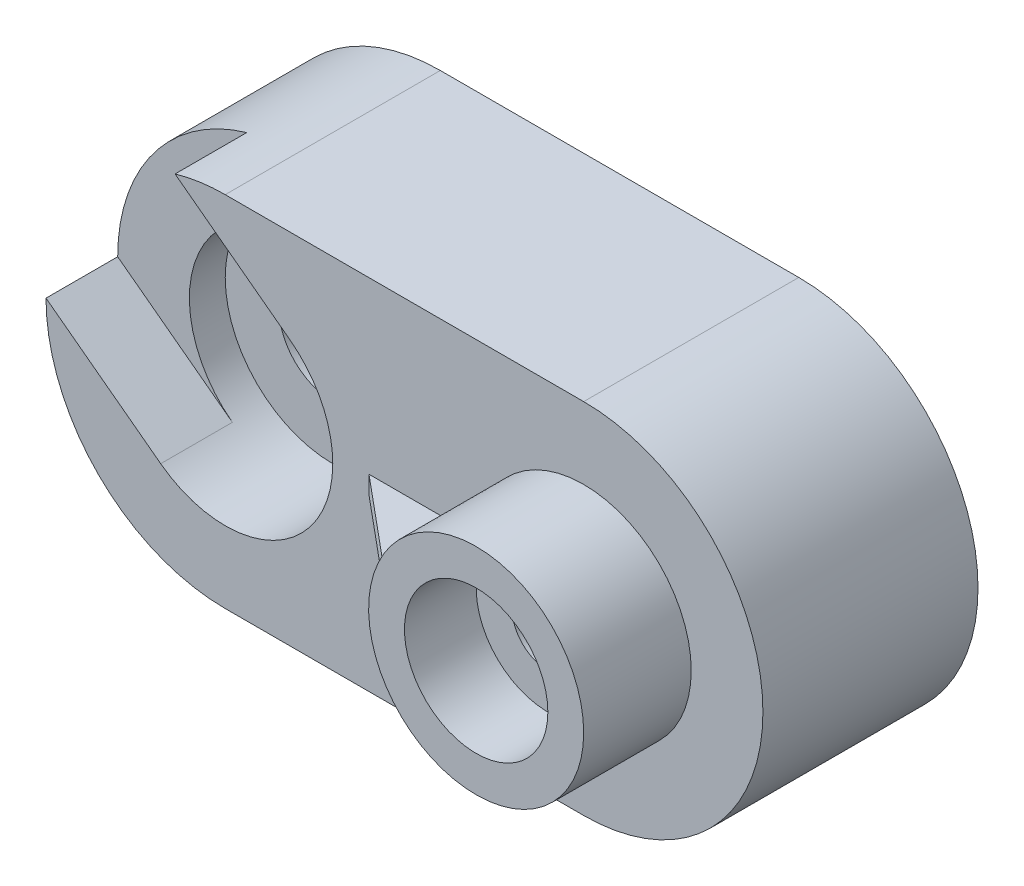
SolidWorks part; units mm, degrees
ref_plane "Front Plane" through (0, 0, 0) normal (0, 0, 1) x (1, 0, 0)
ref_plane "Top Plane" through (0, 0, 0) normal (0, 1, 0) x (1, 0, 0)
ref_plane "Right Plane" through (0, 0, 0) normal (1, 0, 0) x (0, 0, -1)
sketch "Sketch1" plane through (0, 0, 0) normal (0, 0, 1) x (1, 0, 0)
  line L0 (0, 0) -> (100, 0) construction
  line L1 (0, 50) -> (100, 50)
  line L2 (0, -50) -> (100, -50)
  arc A0 (0, 50) -> (0, -50) centre (0, 0) ccw
  arc A1 (100, -50) -> (100, 50) centre (100, 0) ccw
  point P3 (50, 0)
  dimension "D1" = 100
  dimension "D2" = 50
extrude "Boss-Extrude1" add sketch "Sketch1" along normal blind 60
sketch "Sketch2" plane through (0, 0, 0) normal (0, 0, -1) x (-1, 0, 0)
  line L0 (0, 0) -> (-100, 0) construction
  line L1 (0, -30) -> (-100, -30)
  line L2 (0, 30) -> (-100, 30)
  arc A0 (0, -30) -> (0, 30) centre (0, 0) ccw
  arc A1 (-100, 30) -> (-100, -30) centre (-100, 0) ccw
  point P3 (-50, 0)
  dimension "D1" = 100
  dimension "D2" = 30
extrude "Cut-Extrude1" cut sketch "Sketch2" against normal blind 10
sketch "Sketch3" plane through (0, 0, 60) normal (0, 0, 1) x (1, 0, 0)
  circle A0 centre (100, 0) radius 30
  dimension "D1" = 60
extrude "Boss-Extrude2" add sketch "Sketch3" along normal blind 30
sketch "Sketch4" plane through (0, 0, 90) normal (0, 0, 1) x (1, 0, 0)
  circle A0 centre (100, 0) radius 20
  dimension "D1" = 40
extrude "Cut-Extrude3" cut sketch "Sketch4" against normal blind 20
sketch "Sketch5" plane through (0, 0, 70) normal (0, 0, 1) x (1, 0, 0)
  circle A0 centre (100, 0) radius 10
  dimension "D1" = 20
extrude "Cut-Extrude4" cut sketch "Sketch5" against normal blind 129
ref_plane "Plane1" through (100, -50, 0) normal (1, 0, 0) x (0, 0, -1)
sketch "Sketch7" plane through (0, 0, 60) normal (0, 0, 1) x (1, 0, 0)
  line L1 (70.1043, 2.5) -> (40.1043, 2.5)
  line L2 (70.1043, 2.5) -> (70.1043, -2.5)
  line L3 (70.1043, -2.5) -> (40.1043, -2.5)
  line L4 (40.1043, 2.5) -> (40.1043, -2.5)
  circle A0 centre (100, 0) radius 30 construction
  arc A1 (0, 30) -> (0, -30) centre (0, 0) ccw construction
  point P6 (-30, 0)
  dimension "D1" = 5
  dimension "D2" = 2.5
  dimension "D3" = 30
extrude "Boss-Extrude3" add sketch "Sketch7" along normal blind 25
sketch "Sketch8" plane through (0, 0, 60) normal (0, 0, 1) x (1, 0, 0)
  line L0 (18, 24) -> (-14, 48)
  line L1 (-18, -24) -> (-50, 0)
  line L2 (0, 0) -> (-104.1495, 0) construction
  circle A0 centre (0, 0) radius 30
  arc A1 (0, 50) -> (0, -50) centre (0, 0) ccw construction
  dimension "D1" = 60
extrude "Cut-Extrude5" cut sketch "Sketch8" against normal blind 20
sketch "Sketch9" plane through (0, 0, 40) normal (0, 0, 1) x (1, 0, 0)
  circle A0 centre (0, 0) radius 30
  dimension "D1" = 60
extrude "Cut-Extrude6" cut sketch "Sketch9" against normal blind 10
sketch "Sketch10" plane through (0, 0, 30) normal (0, 0, 1) x (1, 0, 0)
  circle A0 centre (0, 0) radius 15
  dimension "D1" = 30
extrude "Cut-Extrude7" cut sketch "Sketch10" against normal blind 155
sketch "Sketch11" plane through (0, -2.5, 0) normal (0, -1, 0) x (1, 0, 0)
  line L0 (40.1043, 60) -> (70.1043, 85)
  line L1 (70.1043, 85) -> (40.1043, 85)
  line L2 (40.1043, 85) -> (40.1043, 60)
extrude "Cut-Extrude8" cut sketch "Sketch11" against normal blind 10
